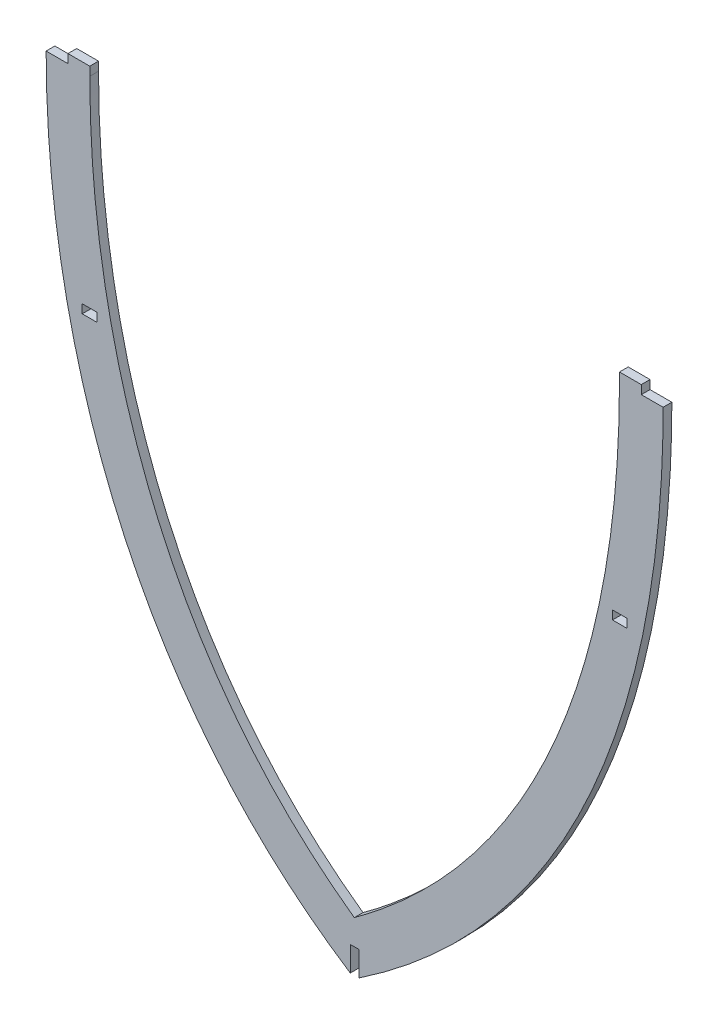
SolidWorks part; units mm, degrees
material "birch 3mm plywood"
ref_plane "Front" through (0, 0, 0) normal (0, 0, 1) x (1, 0, 0)
ref_plane "Top" through (0, 0, 0) normal (0, 1, 0) x (1, 0, 0)
ref_plane "Right" through (0, 0, 0) normal (1, 0, 0) x (0, 0, -1)
sketch "Sketch1" plane through (0, 0, 0) normal (0, 0, 1) x (1, 0, 0)
  line L0 (88.6, -155) -> (88.6, -152) construction
  line L1 (93.6, -155) -> (93.6, -152) construction
  line L2 (98.6, -152) -> (93.6, -152) construction
  line L8 (-88.6, -152) -> (-93.6, -152)
  line L9 (-93.6, -152) -> (-93.6, -155)
  line L10 (-93.6, -155) -> (-88.6, -155)
  line L11 (-88.6, -155) -> (-88.6, -152)
  line L12 (93.6, -152) -> (88.6, -152)
  line L13 (88.6, -152) -> (88.6, -155)
  line L14 (88.6, -155) -> (93.6, -155)
  line L15 (93.6, -155) -> (93.6, -152)
  line L16 (-106, -83) -> (-98.5, -83)
  line L17 (-106, -83) -> (-68.5834, -83) construction
  line L18 (-98.5, -83) -> (-98.5, -80)
  line L19 (-68.5834, -80) -> (-106, -80) construction
  line L20 (-98.5, -80) -> (-91, -80)
  line L21 (-91, -80) -> (-91, -83)
  line L22 (106, -83) -> (98.5, -83)
  line L23 (68.5834, -83) -> (106, -83) construction
  line L24 (98.5, -83) -> (98.5, -80)
  line L25 (106, -80) -> (68.5834, -80) construction
  line L26 (98.5, -80) -> (91, -80)
  line L27 (91, -80) -> (91, -83)
  spline S0 degree 3 poles (-606.6311, -2686.1966) (-1331.3466, 4216.9715) (2505.2437, -3263.0373) (-2575.6318, 1120.6224) knots -6.031856 -6.031856 -6.031856 -6.031856 4.281025 4.281025 4.281025 4.281025 only from (106, -83) to (0, -306.0893) construction
  spline S1 degree 3 poles (689.6249, -2848.8726) (504.5633, 3901.714) (-1758.8386, -3459.7843) (2297.6608, 1523.3776) knots -4.72173 -4.72173 -4.72173 -4.72173 4.086582 4.086582 4.086582 4.086582 only from (-106, -83) to (0, -306.0893) construction
  spline S2 degree 3 poles (106, -83) (106, -174.4433) (74.7629, -256.783) (0, -306.0893) knots 0 0 0 0 1 1 1 1
  spline S3 degree 3 poles (-106, -83) (-106, -171.1717) (-74.7629, -258.4392) (0, -306.0893) knots 0 0 0 0 1 1 1 1
  spline S4 degree 1 poles (-91, -83) (-0.1167, -287.9264) knots 0 0 1 1 construction
  spline S5 degree 1 poles (91, -83) (-0.1167, -287.9264) knots 0 0 1 1 construction
  spline S6 degree 3 poles (-91, -83) (-91, -88.0686) (-90.7842, -98.2205) (-89.4717, -118.3778) (-86.1468, -143.2308) (-79.3681, -172.0711) (-69.7174, -199.532) (-57.1183, -225.2317) (-44.0961, -244.8889) (-32.112, -259.4019) (-22.3248, -269.6427) (-13.4811, -277.6134) (-5.9927, -283.6258) (-2.0894, -286.5211) (-0.1167, -287.9264) knots 0 0 0 0 0.059983 0.119967 0.239934 0.359901 0.479868 0.599835 0.719802 0.779785 0.839769 0.899752 0.929744 0.959735 0.959735 0.959735 0.959735
  spline S7 degree 3 poles (-0.1167, -287.9264) (1.8708, -286.4802) (5.8114, -283.5064) (13.356, -277.3846) (22.2576, -269.3453) (32.0901, -259.1217) (44.1097, -244.7411) (57.1396, -225.4116) (69.7252, -200.2046) (79.363, -173.1605) (85.0093, -149.2619) (88.136, -129.4393) (89.7964, -114.2526) (90.6189, -101.351) (90.9458, -90.91) (91, -85.632) (91, -83) knots 0 0 0 0 0.030008 0.060016 0.120032 0.180048 0.240064 0.360096 0.480129 0.600161 0.720193 0.780209 0.840225 0.900241 0.930249 0.960257 0.960257 0.960257 0.960257
  dimension "D2" = 7.5
  dimension "D3" = 7.5
  dimension "D1" = 15
extrude "Boss-Extrude1" add sketch "Sketch1" along normal mid plane 3
sketch "Sketch2" plane through (0, 0, 1.5) normal (0, 0, 1) x (1, 0, 0)
  line L0 (-1.5, -296.5952) -> (1.5, -296.5952)
  line L1 (1.5, -296.5952) -> (1.5, -306.0893)
  line L2 (1.5, -306.0893) -> (-1.5, -306.0893)
  line L3 (1.5, -306.0893) -> (-1.5, -306.0893) construction
  line L4 (-1.5, -83) -> (-1.5, -306.0893) construction
  line L5 (-1.5, -306.0893) -> (-1.5, -296.5952)
extrude "Cut-Extrude1" cut sketch "Sketch2" against normal blind 3
